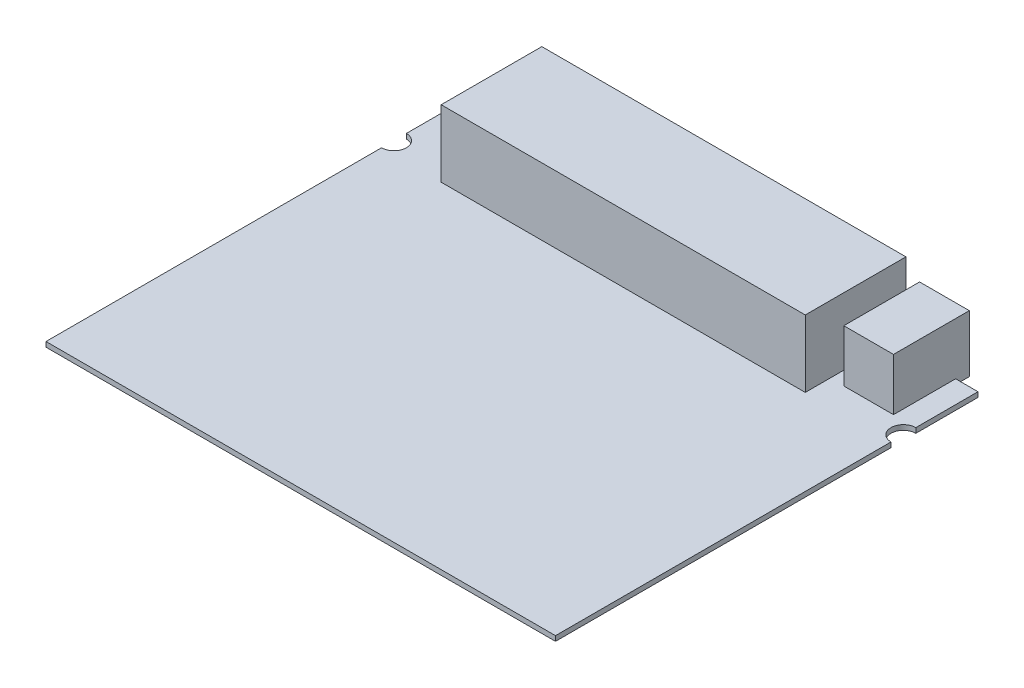
SolidWorks part; units mm, degrees
ref_plane "Front Plane" through (0, 0, 0) normal (0, 0, 1) x (1, 0, 0)
ref_plane "Top Plane" through (0, 0, 0) normal (0, 1, 0) x (1, 0, 0)
ref_plane "Right Plane" through (0, 0, 0) normal (1, 0, 0) x (0, 0, -1)
sketch "Sketch1" plane through (0, 0, 0) normal (0, 1, 0) x (1, 0, 0)
  line L0 (52.07, -43.18) -> (52.07, 25.4) construction
  line L1 (-52.07, -43.18) -> (52.07, -43.18)
  line L2 (-52.07, -43.18) -> (-52.07, 25.4)
  line L3 (-39.878, 45.974) -> (34.544, 45.974)
  line L4 (52.07, -43.18) -> (52.07, 25.4)
  line L5 (-52.07, -43.18) -> (52.07, 43.18) construction
  line L6 (-52.07, 43.18) -> (52.07, -43.18) construction
  line L7 (52.07, 43.18) -> (47.498, 43.18)
  line L8 (52.07, 43.18) -> (52.07, 30.48) construction
  line L9 (52.07, -43.18) -> (52.07, 25.4) construction
  line L10 (0, 0) -> (0, 60.9791) construction
  line L11 (0, 0) -> (0, -67.902) construction
  line L12 (52.07, 30.48) -> (52.07, 43.18) construction
  line L13 (52.07, 30.48) -> (52.07, 43.18)
  line L14 (-52.07, 30.48) -> (-52.07, 43.18)
  line L15 (52.07, -43.18) -> (46.9577, -43.18) construction
  line L16 (52.07, 30.48) -> (34.544, 30.48) construction
  line L17 (-52.07, 30.48) -> (-39.878, 30.48) construction
  line L18 (-52.07, 25.4) -> (52.07, 25.4) construction
  line L19 (-39.878, 30.48) -> (-39.878, 25.4) construction
  line L20 (34.544, 30.48) -> (34.544, 25.4) construction
  line L21 (52.07, 30.48) -> (47.498, 30.48) construction
  line L22 (-39.878, 25.4) -> (34.544, 25.4)
  line L23 (-39.878, 25.4) -> (-39.878, 45.974)
  line L24 (-39.878, 45.974) -> (34.544, 45.974)
  line L25 (34.544, 25.4) -> (34.544, 45.974)
  line L26 (47.498, 30.48) -> (37.338, 30.48) construction
  line L27 (37.338, 45.974) -> (47.498, 45.974)
  line L28 (47.498, 30.48) -> (37.338, 30.48)
  line L29 (47.498, 30.48) -> (47.498, 45.974)
  line L30 (47.498, 45.974) -> (37.338, 45.974)
  line L31 (37.338, 30.48) -> (37.338, 45.974)
  line L32 (-39.878, 43.18) -> (-52.07, 43.18)
  line L33 (37.338, 43.18) -> (34.544, 43.18)
  line L34 (-39.878, 43.18) -> (-39.878, 25.4)
  line L35 (34.544, 43.18) -> (34.544, 25.4)
  arc A0 (52.07, 30.48) -> (52.07, 25.4) centre (52.07, 27.94) ccw
  arc A1 (-52.07, 30.48) -> (-52.07, 25.4) centre (-52.07, 27.94) cw
  point P0 (0, 0)
  dimension "D2" = 104.14
  dimension "D3" = 86.36
  dimension "D4" = 12.7
  dimension "D5" = 68.58
  dimension "D6" = 5.1123
  dimension "D7" = 17.526
  dimension "D8" = 12.192
  dimension "D9" = 4.572
  dimension "D10" = 10.16
  dimension "D11" = 20.574
sketch "Sketch2" plane through (0, 0, 0) normal (0, 1, 0) x (1, 0, 0)
  line L0 (-39.878, 25.4) -> (-39.878, 45.974) construction
  line L1 (-39.878, 25.4) -> (-39.878, 45.974)
  line L2 (-39.878, 45.974) -> (34.544, 45.974) construction
  line L3 (-39.878, 45.974) -> (34.544, 45.974)
  line L4 (-39.878, 25.4) -> (34.544, 25.4) construction
  line L5 (34.544, 25.4) -> (34.544, 45.974) construction
  line L6 (-39.878, 25.4) -> (34.544, 25.4)
  line L7 (34.544, 25.4) -> (34.544, 45.974)
extrude "Boss-Extrude3" add sketch "Sketch2" along normal blind 14.732
sketch "Sketch7" plane through (0, 0, 0) normal (0, 1, 0) x (1, 0, 0)
  line L0 (37.338, 30.48) -> (37.338, 45.974) construction
  line L1 (37.338, 45.974) -> (47.498, 45.974) construction
  line L2 (47.498, 30.48) -> (47.498, 45.974) construction
  line L3 (47.498, 30.48) -> (37.338, 30.48) construction
  line L4 (37.338, 30.48) -> (37.338, 45.974)
  line L5 (37.338, 45.974) -> (47.498, 45.974)
  line L6 (47.498, 30.48) -> (47.498, 45.974)
  line L7 (47.498, 30.48) -> (37.338, 30.48)
extrude "Boss-Extrude4" add sketch "Sketch7" along normal blind 11.684 separate body
sketch "Sketch9" plane through (0, 0, 0) normal (0, 1, 0) x (1, 0, 0)
  line L0 (-39.878, 43.18) -> (-52.07, 43.18) construction
  line L1 (-52.07, 30.48) -> (-52.07, 43.18) construction
  line L2 (-39.878, 25.4) -> (-39.878, 45.974) construction
  line L3 (-52.07, -43.18) -> (-52.07, 25.4) construction
  line L4 (-52.07, -43.18) -> (52.07, -43.18) construction
  line L5 (52.07, -43.18) -> (52.07, 25.4) construction
  line L6 (52.07, 43.18) -> (47.498, 43.18) construction
  line L7 (52.07, 30.48) -> (52.07, 43.18) construction
  line L8 (47.498, 30.48) -> (47.498, 45.974) construction
  line L9 (47.498, 30.48) -> (37.338, 30.48) construction
  line L10 (37.338, 30.48) -> (37.338, 45.974) construction
  line L11 (37.338, 43.18) -> (34.544, 43.18) construction
  line L12 (34.544, 25.4) -> (34.544, 45.974) construction
  line L13 (-39.878, 25.4) -> (34.544, 25.4) construction
  line L14 (-39.878, 43.18) -> (-52.07, 43.18)
  line L15 (-52.07, 30.48) -> (-52.07, 43.18)
  line L16 (-39.878, 25.4) -> (-39.878, 43.18)
  line L17 (-52.07, -43.18) -> (-52.07, 25.4)
  line L18 (-52.07, -43.18) -> (52.07, -43.18)
  line L19 (52.07, -43.18) -> (52.07, 25.4)
  line L20 (52.07, 43.18) -> (47.498, 43.18)
  line L21 (52.07, 30.48) -> (52.07, 43.18)
  line L22 (47.498, 30.48) -> (47.498, 43.18)
  line L23 (47.498, 30.48) -> (37.338, 30.48)
  line L24 (37.338, 30.48) -> (37.338, 43.18)
  line L25 (37.338, 43.18) -> (34.544, 43.18)
  line L26 (34.544, 25.4) -> (34.544, 43.18)
  line L27 (-39.878, 25.4) -> (34.544, 25.4)
  arc A0 (-52.07, 25.4) -> (-52.07, 30.48) centre (-52.07, 27.94) ccw construction
  arc A1 (52.07, 30.48) -> (52.07, 25.4) centre (52.07, 27.94) ccw construction
  arc A2 (-52.07, 25.4) -> (-52.07, 30.48) centre (-52.07, 27.94) ccw
  arc A3 (52.07, 30.48) -> (52.07, 25.4) centre (52.07, 27.94) ccw
  point P0 (-39.878, 43.18)
  point P2 (-39.878, 25.4)
extrude "Boss-Extrude5" add sketch "Sketch9" along normal blind 1.016
